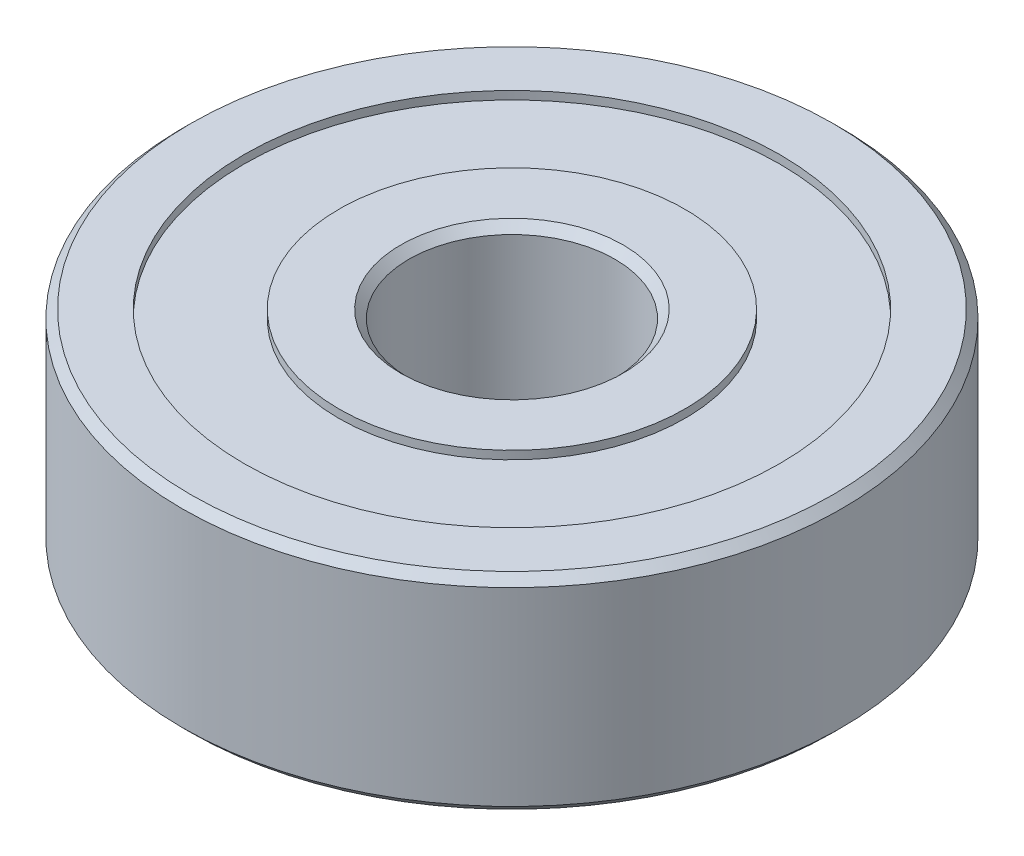
SolidWorks part; units mm, degrees
ref_plane "Front Plane" through (0, 0, 0) normal (0, 0, 1) x (1, 0, 0)
ref_plane "Top Plane" through (0, 0, 0) normal (0, 1, 0) x (1, 0, 0)
ref_plane "Right Plane" through (0, 0, 0) normal (1, 0, 0) x (0, 0, -1)
sketch "Sketch1" plane through (0, 0, 0) normal (0, 1, 0) x (1, 0, 0)
  circle A0 centre (0, 0) radius 8
  circle A1 centre (0, 0) radius 2.5
  dimension "D1" = 16
  dimension "D2" = 5
extrude "Boss-Extrude1" add sketch "Sketch1" along normal blind 5
sketch "Sketch2" plane through (0, 5, 0) normal (0, 1, 0) x (1, 0, 0)
  circle A0 centre (0, 0) radius 4.2
  circle A1 centre (0, 0) radius 6.5
  dimension "D1" = 13
  dimension "D2" = 8.4
extrude "Cut-Extrude1" cut sketch "Sketch2" against normal blind 0.2
sketch "Sketch3" plane through (0, 0, 0) normal (0, -1, 0) x (1, 0, 0)
  circle A0 centre (0, 0) radius 4.2 construction
  circle A1 centre (0, 0) radius 6.5
  circle A3 centre (0, 0) radius 4.2
  circle A6 centre (0, 0) radius 6.5
  dimension "D1" = 0
extrude "Cut-Extrude2" cut sketch "Sketch3" against normal blind 0.2
chamfer "Chamfer1" distance 0.2 angle 45 4 edges at (0, 5, 8) (0, 0, 8) (0, 5, 2.5) (0, 0, 2.5)
